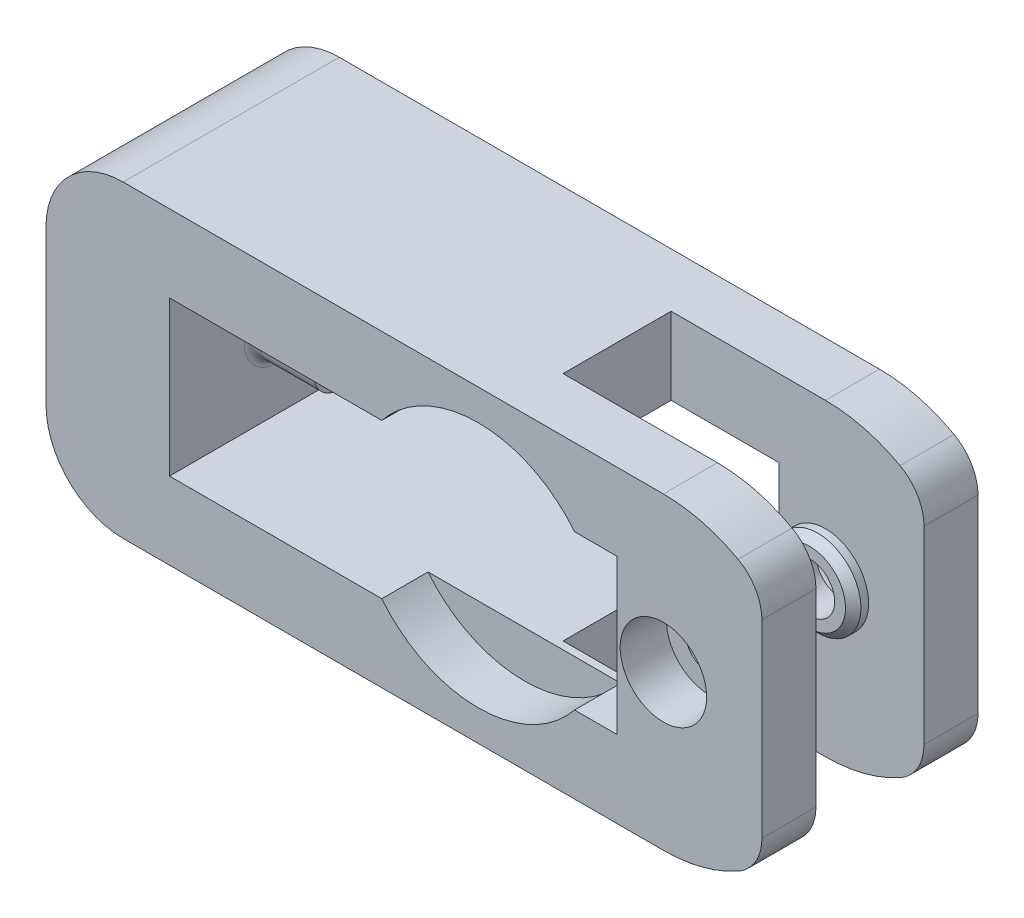
SolidWorks part; units mm, degrees
ref_plane "Ön Düzlem" through (0, 0, 0) normal (0, 0, 1) x (1, 0, 0)
ref_plane "Üst Düzlem" through (0, 0, 0) normal (0, 1, 0) x (1, 0, 0)
ref_plane "Sağ Düzlem" through (0, 0, 0) normal (1, 0, 0) x (0, 0, -1)
sketch "Çizim1" plane through (0, 0, 0) normal (0, 0, 1) x (1, 0, 0)
  line L0 (-28.3719, 20) -> (11.6281, 20)
  line L1 (-28.3719, 20) -> (-28.3719, 0)
  line L2 (-28.3719, 0) -> (11.6281, 0)
  line L3 (11.6281, 20) -> (11.6281, 15)
  line L4 (11.6281, 0) -> (11.6281, 5)
  line L5 (11.6281, 5) -> (-20.3719, 5)
  line L6 (-20.3719, 5) -> (-20.3719, 15)
  line L7 (-20.3719, 15) -> (11.6281, 15)
  dimension "D1" = 40
  dimension "D2" = 8
extrude "Yükseklik-Ekstrüzyon1" add sketch "Çizim1" along normal blind 14
fillet "Radyus1" radius 5 2 edges at (-28.3719, 0, 7) (-28.3719, 20, 7)
sketch "Çizim3" plane through (0, 20, 0) normal (0, 1, 0) x (1, 0, 0)
  line L0 (11.6281, 0) -> (-23.3719, 0) construction
  line L4 (1.6281, -3.5) -> (11.6281, -3.5)
  line L5 (11.6281, -14) -> (11.6281, 0) construction
  line L6 (11.6281, -3.5) -> (11.6281, -10.5)
  line L7 (1.6281, -3.5) -> (1.6281, -10.5)
  line L9 (11.6281, -10.5) -> (1.6281, -10.5)
  dimension "D1" = 3.5
extrude "Kes-Ekstrüzyon2" cut sketch "Çizim3" against normal blind 20
sketch "Çizim4" plane through (0, 0, 14) normal (0, 0, 1) x (1, 0, 0)
  line L0 (11.6281, 0) -> (11.6281, 5) construction
  line L1 (18.012, 17.6971) -> (18.012, 2.3029)
  arc A0 (18.012, 17.6971) -> (18.012, 2.3029) centre (11.6281, 10) ccw
  dimension "D1" = 0
extrude "Yükseklik-Ekstrüzyon2" add sketch "Çizim4" against normal blind 3.5
sketch "Çizim5" plane through (0, 0, 0) normal (0, 0, -1) x (-1, 0, 0)
  line L0 (-18.012, 17.6971) -> (-18.012, 2.3029)
  arc A0 (-18.012, 2.3029) -> (-18.012, 17.6971) centre (-11.6281, 10) ccw
extrude "Yükseklik-Ekstrüzyon3" add sketch "Çizim5" against normal blind 3.5
sketch "Çizim6" plane through (0, 0, 10.5) normal (0, 0, -1) x (-1, 0, 0)
  circle A0 centre (-11.6281, 10) radius 2.8
  circle A1 centre (-11.6281, 10) radius 1.6
extrude "Yükseklik-Ekstrüzyon4" add sketch "Çizim6" along normal blind 1
sketch "Çizim7" plane through (0, 0, 3.5) normal (0, 0, 1) x (1, 0, 0)
  circle A0 centre (11.6281, 10) radius 2.8
  circle A1 centre (11.6281, 10) radius 1.6
extrude "Yükseklik-Ekstrüzyon5" add sketch "Çizim7" along normal blind 1
chamfer "Pah1" distance 0.5 angle 45 2 edges at (14.4281, 10, 4.5) (8.8281, 10, 9.5)
sketch "Çizim8" plane through (0, 0, 14) normal (0, 0, 1) x (1, 0, 0)
  line L0 (-20.3719, 15) -> (8.6281, 15)
  line L1 (8.6281, 15) -> (8.6281, 5)
  line L2 (8.6281, 5) -> (-20.3719, 5)
  line L4 (-20.3719, 15) -> (-20.3719, 5)
extrude "Kes-Ekstrüzyon3" cut sketch "Çizim8" against normal blind 15
sketch "Çizim9" plane through (0, 0, 14) normal (0, 0, 1) x (1, 0, 0)
  circle A0 centre (11.6281, 10) radius 2.8
extrude "Kes-Ekstrüzyon5" cut sketch "Çizim9" against normal blind 3
sketch "Çizim10" plane through (0, 0, 0) normal (0, 0, -1) x (-1, 0, 0)
  line L1 (-11.6281, 13.15) -> (-14.3561, 11.575)
  line L2 (-14.3561, 11.575) -> (-14.3561, 8.425)
  line L3 (-14.3561, 8.425) -> (-11.6281, 6.85)
  line L4 (-11.6281, 6.85) -> (-8.9001, 8.425)
  line L5 (-8.9001, 8.425) -> (-8.9001, 11.575)
  line L6 (-8.9001, 11.575) -> (-11.6281, 13.15)
  circle A0 centre (-11.6281, 10) radius 2.728 construction
extrude "Kes-Ekstrüzyon6" cut sketch "Çizim10" against normal blind 2.5
sketch "Çizim11" plane through (0, 0, 11) normal (0, 0, 1) x (1, 0, 0)
  circle A0 centre (11.6281, 10) radius 1.6
extrude "Kes-Ekstrüzyon7" cut sketch "Çizim11" against normal blind 10
sketch "Çizim12" plane through (-20.3719, 0, 0) normal (1, 0, 0) x (0, 0, -1)
  circle A0 centre (-7, 10) radius 1.65
extrude "Yükseklik-Ekstrüzyon6" add sketch "Çizim12" along normal blind 4
fillet "Radyus2" radius 0.5 1 edges at (-20.3719, 10, 8.65)
ref_plane "Düzlem1" through (0, 0, 7) normal (0, 0, -1) x (-1, 0, 0)
sketch "Çizim14" plane through (0, 0, 7) normal (0, 0, -1) x (-1, 0, 0)
  line L0 (32.3719, 16) -> (32.3719, 4)
  line L2 (28.3719, 15) -> (28.3719, 5) construction
  arc A0 (32.3719, 4) -> (32.3719, 16) centre (32.3719, 10) ccw
  point P2 (28.3719, 10)
  dimension "D1" = 4
revolve "Kes-Döndür1" cut sketch "Çizim14" angle 360 about L0
fillet "Radyus5" radius 1 1 edges at (-28.3719, 10, 2.5279)
fillet "Radyus7" radius 3 4 edges at (18.012, 17.6971, 1.75) (18.012, 2.3029, 1.75) (18.012, 2.3029, 12.25) (18.012, 17.6971, 12.25)
sketch "Çizim15" plane through (0, 0, 14) normal (0, 0, 1) x (1, 0, 0)
  line L0 (8.6281, 5) -> (8.6281, 15) construction
  circle A0 centre (-0.3719, 10) radius 8
  dimension "D1" = 9
extrude "Kes-Ekstrüzyon8" cut sketch "Çizim15" against normal blind 3
